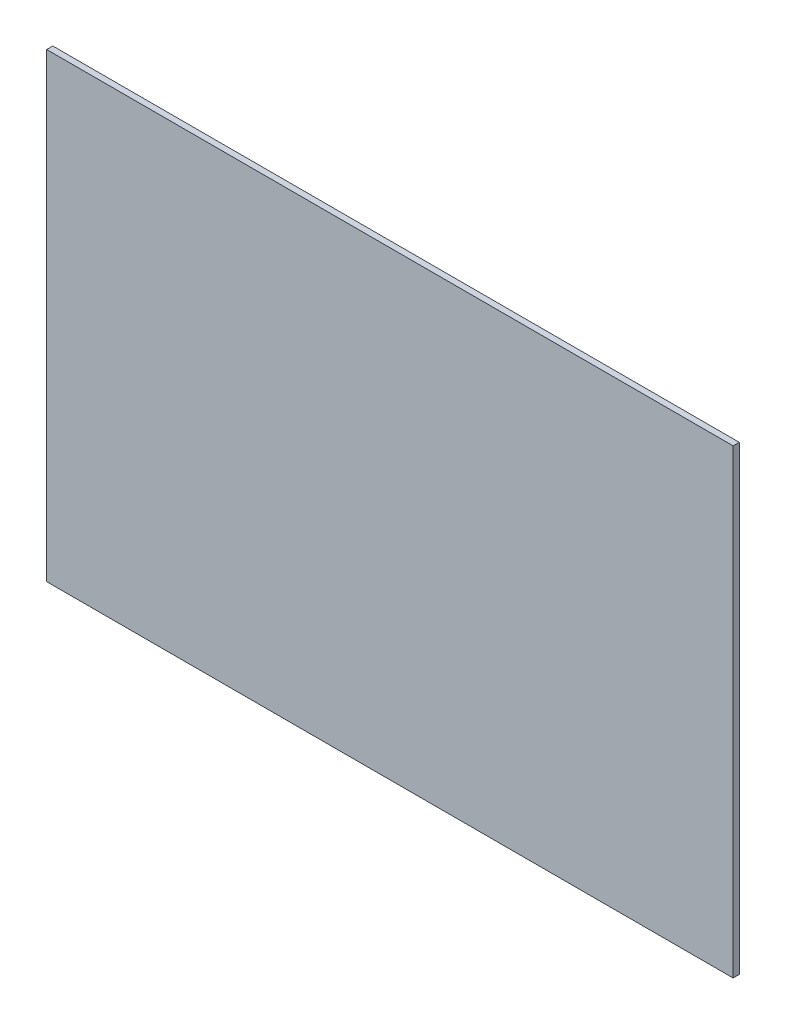
SolidWorks part; units mm, degrees
ref_plane "Front Plane" through (0, 0, 0) normal (0, 0, 1) x (1, 0, 0)
ref_plane "Top Plane" through (0, 0, 0) normal (0, 1, 0) x (1, 0, 0)
ref_plane "Right Plane" through (0, 0, 0) normal (1, 0, 0) x (0, 0, -1)
sketch "Sketch1" plane through (0, 0, 0) normal (0, 0, 1) x (1, 0, 0)
  line L1 (335.7562, 225.425) -> (-335.7563, 225.425)
  line L2 (335.7562, 225.425) -> (335.7562, -225.425)
  line L3 (335.7562, -225.425) -> (-335.7563, -225.425)
  line L4 (-335.7563, 225.425) -> (-335.7563, -225.425)
  line L5 (335.7562, 225.425) -> (-335.7563, -225.425) construction
  line L6 (335.7562, -225.425) -> (-335.7563, 225.425) construction
  point P0 (0, 0)
  dimension "D1" = 450.85
  dimension "D2" = 671.5125
extrude "Boss-Extrude1" add sketch "Sketch1" along normal mid plane 6
sketch "Sketch2" plane through (0, 0, 3) normal (0, 0, 1) x (1, 0, 0)
  line L0 (300.8313, 176.9479) -> (-300.8313, 176.9479)
  line L5 (0, 176.9479) -> (0, 0) construction
  line L7 (-300.8313, 176.9479) -> (-300.8312, -164.3646)
  line L8 (300.8313, -164.3646) -> (-300.8312, -164.3646)
  line L9 (300.8313, 176.9479) -> (300.8313, -164.3646)
  line L12 (-335.7563, 225.425) -> (-335.7563, -225.425)
  line L13 (335.7562, 225.425) -> (-335.7563, 225.425)
  line L14 (335.7562, -225.425) -> (335.7562, 225.425)
  line L15 (-335.7563, -225.425) -> (335.7562, -225.425)
  line L16 (-335.7563, 225.425) -> (-335.7563, -225.425)
  line L17 (335.7562, 225.425) -> (-335.7563, 225.425)
  line L18 (335.7562, -225.425) -> (335.7562, 225.425)
  line L19 (-335.7563, -225.425) -> (335.7562, -225.425)
  point P0 (0, 0)
  dimension "D1" = 601.6625
  dimension "D3" = 341.3125
  dimension "D4" = 48.4771
  dimension "D2" = 0
extrude "Boss-Extrude2" [suppressed] add sketch "Sketch2" along normal blind 0.254 separate body
